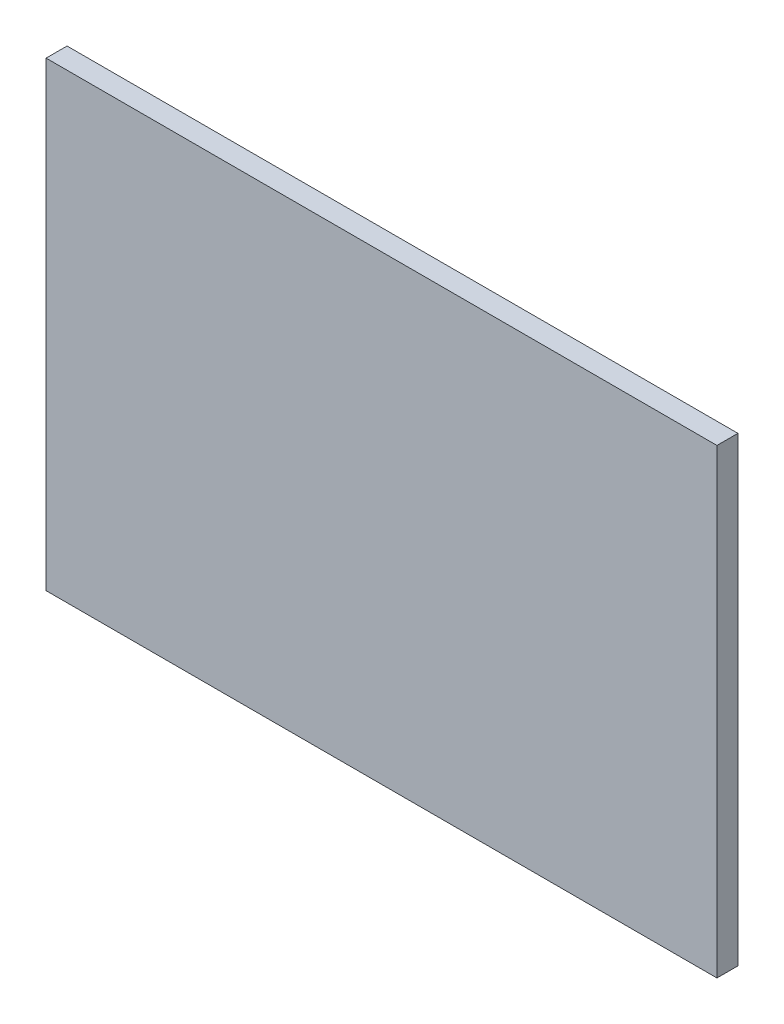
SolidWorks part; units mm, degrees
ref_plane "Front Plane" through (0, 0, 0) normal (0, 0, 1) x (1, 0, 0)
ref_plane "Top Plane" through (0, 0, 0) normal (0, 1, 0) x (1, 0, 0)
ref_plane "Right Plane" through (0, 0, 0) normal (1, 0, 0) x (0, 0, -1)
sketch "Sketch1" plane through (0, 0, 0) normal (0, 0, 1) x (1, 0, 0)
  line L1 (0, 0) -> (800, 0)
  line L2 (0, 0) -> (0, 550)
  line L3 (0, 550) -> (800, 550)
  line L4 (800, 0) -> (800, 550)
  dimension "D1" = 550
  dimension "D2" = 800
extrude "Boss-Extrude1" add sketch "Sketch1" along normal blind 25
